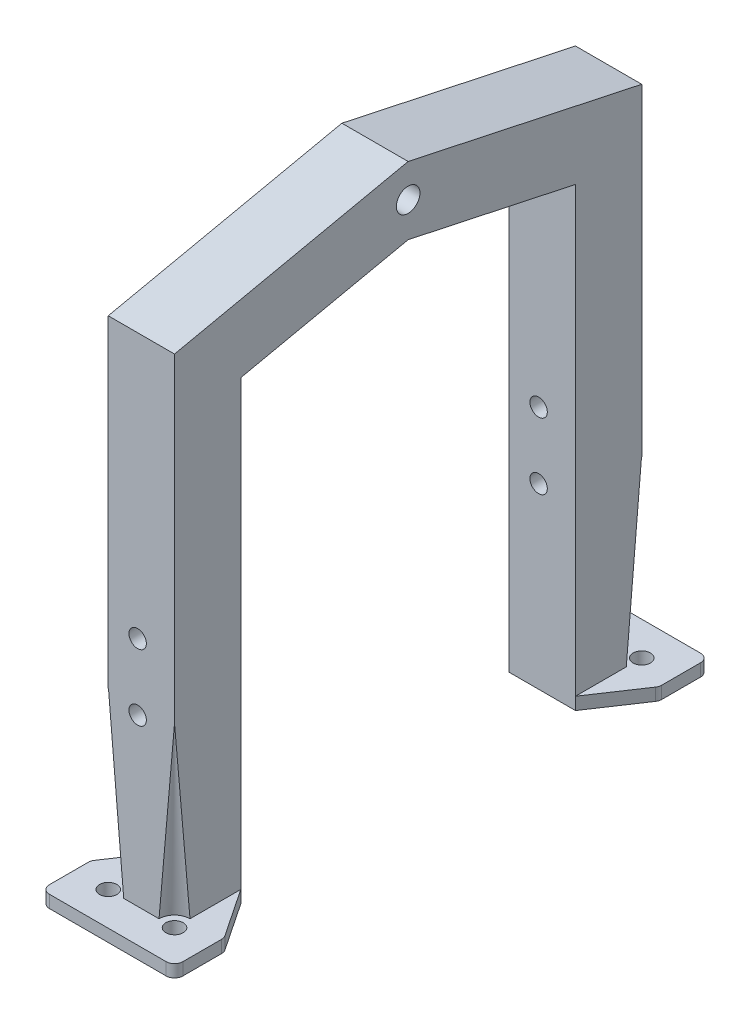
SolidWorks part; units mm, degrees
ref_plane "Front Plane" through (0, 0, 0) normal (0, 0, 1) x (1, 0, 0)
ref_plane "Top Plane" through (0, 0, 0) normal (0, 1, 0) x (1, 0, 0)
ref_plane "Right Plane" through (0, 0, 0) normal (1, 0, 0) x (0, 0, -1)
sketch "Sketch1" plane through (0, 0, 0) normal (1, 0, 0) x (0, 0, -1)
  line L0 (0, -1165.1636) -> (0, 57093.018) construction
  line L2 (-56.4, 122.9405) -> (-56.4, 0)
  line L3 (-56.4, 0) -> (-40.4, 0)
  line L4 (-40.4, 0) -> (-40.4, 110)
  line L6 (40.4, 0) -> (40.4, 110)
  line L7 (56.4, 0) -> (40.4, 0)
  line L8 (56.4, 122.9405) -> (56.4, 0)
  line L9 (-56.4, 122.9405) -> (0, 135)
  line L10 (0, 135) -> (56.4, 122.9405)
  line L11 (40.4, 110) -> (0, 118.6383)
  line L12 (0, 118.6383) -> (-40.4, 110)
  point P10 (0, 90)
  point P13 (0, 106)
  dimension "D1" = 16
  dimension "D3" = 110
  dimension "D4" = 112.8
  dimension "D2" = 135
  dimension "D5" = 16
extrude "Boss-Extrude1" add sketch "Sketch1" along normal mid plane 16
sketch "Sketch2" plane through (0, 0, 0) normal (0, -1, 0) x (1, 0, 0)
  circle A0 centre (-8, -56.4) radius 4
  circle A1 centre (8, -56.4) radius 4
  dimension "D1" = 8
extrude "Cut-Extrude1" cut sketch "Sketch2" against normal blind 45 draft 5 and the other way through all
sketch "Sketch3" plane through (0, 0, 0) normal (0, 1, 0) x (1, 0, 0)
  line L0 (4, 56.4) -> (-4, 56.4) construction
  line L1 (-8, 40.4) -> (8, 40.4)
  line L2 (-16.1, 52.5) -> (-16.1, 64.5)
  line L3 (-16.1, 64.5) -> (16.1, 64.5)
  line L4 (16.1, 52.5) -> (16.1, 64.5)
  line L6 (8, 40.4) -> (16.1, 52.5)
  line L7 (-8, 40.4) -> (-16.1, 52.5)
  line L8 (16.1, 52.5) -> (-16.1, 52.5) construction
  circle A0 centre (-8, 56.4) radius 2.1
  circle A1 centre (8, 56.4) radius 2.1
  point P25 (0, 56.4)
  point P26 (0, 52.5)
  dimension "D1" = 4.2
  dimension "D2" = 6
  dimension "D3" = 6
  dimension "D4" = 12
extrude "Boss-Extrude2" add sketch "Sketch3" along normal blind 3
fillet "Fillet1" radius 2 4 edges at (16.1, 1.5, -52.5) (-16.1, 1.5, -52.5) (16.1, 1.5, -64.5) (-16.1, 1.5, -64.5)
sketch "Sketch4" plane through (0, 0, -56.4) normal (0, 0, -1) x (-1, 0, 0)
  line L0 (0.9, 43) -> (0.9, 59) construction
  line L1 (4.2625, 3) -> (-4.2625, 3) construction
  line L4 (8, 45) -> (8, 122.9405) construction
  circle A0 centre (0.9, 59) radius 2.1
  circle A1 centre (0.9, 43) radius 2.1
  dimension "D1" = 16
  dimension "D2" = 4.2
  dimension "D3" = 40
  dimension "D4" = 5
extrude "Cut-Extrude2" cut sketch "Sketch4" against normal up to next (16 mm away)
mirror "Mirror1" about plane through (0, 0, 0) normal (0, 0, 1) of "Cut-Extrude2", "Cut-Extrude1", "Boss-Extrude2", "Fillet1"
sketch "Sketch5" plane through (8, 0, 0) normal (1, 0, 0) x (0, 0, -1)
  circle A0 centre (0, 127) radius 2.85
  dimension "D1" = 5.7
extrude "Cut-Extrude3" cut sketch "Sketch5" against normal through all
equation "\"width\"= 24"
equation "\"thk\"= 3"
equation "\"holesize\"= 4.2"
equation "\"holedistance\"= ( 20 + 12 ) / 2"
equation "\"threaded_hole\"= 3.9"
equation "\"fillet_radius\"= 2"
equation "\"ground_clearance\"= 25"
equation "\"tire_thk\"= 3"
equation "\"innerwheel_diam\" = \"wheel_diam\"-2*\"tire_thk\""
equation "\"innerwheel_thk\"= 8"
equation "\"wheel_diam\"= 2*(\"width\"/2+\"ground_clearance\")"
equation "\"coloursensor_holesize\"= 2.65"
equation "\"hole_to_edge\" = 4"
equation "\"D1@Sketch3\"=\"holesize\""
equation "\"D3@Sketch3\"=\"D2@Sketch3\""
equation "\"D1@Fillet1\"=\"fillet_radius\""
equation "\"D1@Sketch1\"=\"holedistance\""
equation "\"D1@Boss-Extrude1\"=\"holedistance\""
equation "\"D1@Sketch4\"=\"holedistance\""
equation "\"D2@Sketch4\"=\"holesize\""
equation "\"D5@Sketch1\"=\"D1@Sketch1\""
